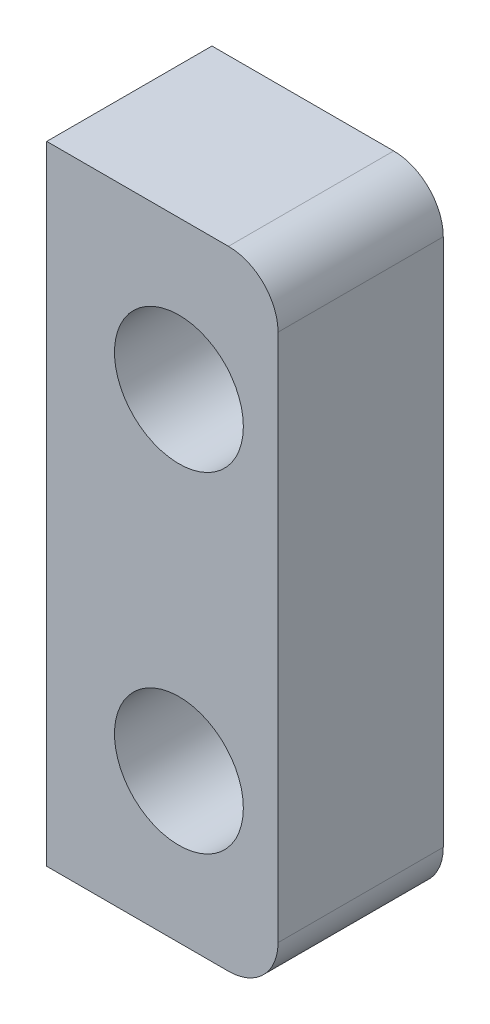
SolidWorks part; units mm, degrees
ref_plane "Front Plane" through (0, 0, 0) normal (0, 0, 1) x (1, 0, 0)
ref_plane "Top Plane" through (0, 0, 0) normal (0, 1, 0) x (1, 0, 0)
ref_plane "Right Plane" through (0, 0, 0) normal (1, 0, 0) x (0, 0, -1)
sketch "Sketch1" plane through (0, 0, 0) normal (0, 0, 1) x (1, 0, 0)
  line L0 (20, -9.5) -> (20, 9.5)
  line L1 (20, -9.5) -> (25.5, -9.5)
  line L2 (20, 9.5) -> (25.5, 9.5)
  line L3 (27, -8) -> (27, 8)
  line L4 (27, 0) -> (20, 0) construction
  line L5 (24, -9.5) -> (24, 9.5) construction
  circle A1 centre (24, -5) radius 1.95
  circle A2 centre (24, 5) radius 1.95
  arc A6 (25.5, -9.5) -> (27, -8) centre (25.5, -8) ccw
  arc A7 (25.5, 9.5) -> (27, 8) centre (25.5, 8) cw
  point P6 (0, 0)
  point P7 (0, 0)
  point P8 (0, 0)
  point P9 (24, -5)
  point P10 (24, 5)
  point P11 (0, 0)
  dimension "D2" = 5
  dimension "D3" = 1.3667
  dimension "D4" = 3.9
  dimension "D1" = 1.5
  dimension "D6" = 3.9
  dimension "D5" = 2.6333
  dimension "D7" = 5
extrude "Boss-Extrude2" add sketch "Sketch1" against normal blind 5
